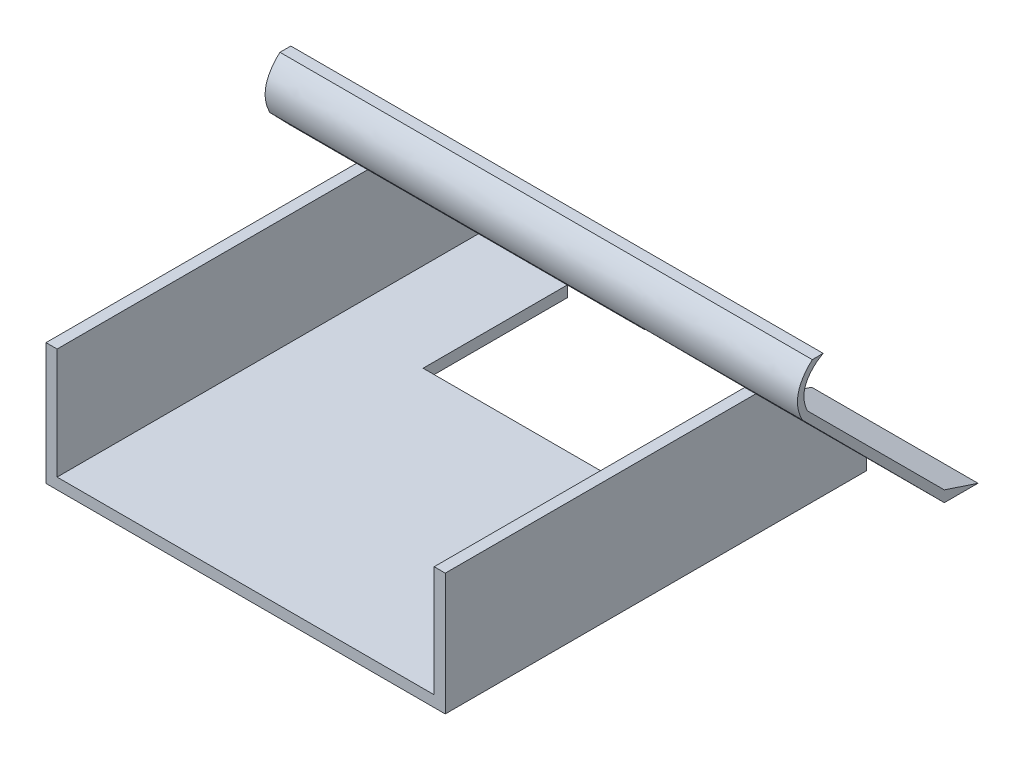
SolidWorks part; units mm, degrees
ref_plane "Front Plane" through (0, 0, 0) normal (0, 0, 1) x (1, 0, 0)
ref_plane "Top Plane" through (0, 0, 0) normal (0, 1, 0) x (1, 0, 0)
ref_plane "Right Plane" through (0, 0, 0) normal (1, 0, 0) x (0, 0, -1)
sketch "Sketch2" plane through (0, 0, 0) normal (0, 1, 0) x (1, 0, 0)
  line L1 (-90, 95) -> (90, 95)
  line L2 (-90, 95) -> (-90, -95)
  line L3 (-90, -95) -> (90, -95)
  line L4 (90, 95) -> (90, -95)
  line L5 (-90, 95) -> (90, -95) construction
  line L6 (-90, -95) -> (90, 95) construction
  point P0 (0, 0)
  dimension "D1" = 180
  dimension "D2" = 190
extrude "Boss-Extrude3" add sketch "Sketch2" along normal blind 5
sketch "Sketch4" plane through (0, 5, 0) normal (0, 1, 0) x (1, 0, 0)
  line L0 (-90, -95) -> (90, -95) construction
  line L3 (-90, 95) -> (-85, 95)
  line L4 (-90, 95) -> (-90, -95)
  line L5 (-90, -95) -> (-85, -95)
  line L6 (-85, 95) -> (-85, -95)
  line L8 (90, 95) -> (85, 95)
  line L9 (90, 95) -> (90, -95)
  line L10 (90, -95) -> (85, -95)
  line L11 (85, 95) -> (85, -95)
  dimension "D1" = 5
  dimension "D2" = 5
extrude "Boss-Extrude4" add sketch "Sketch4" along normal blind 50
sketch "Sketch5" plane through (-90, 0, 0) normal (-1, 0, 0) x (0, 0, 1)
  line L0 (-95, 5) -> (-45, 55)
  line L1 (-95, 55) -> (95, 55) construction
  line L2 (-45, 55) -> (-95, 55)
  line L3 (-95, 55) -> (-95, 5)
extrude "Cut-Extrude1" cut sketch "Sketch5" against normal blind 213
sketch "Sketch6" plane through (-90, 0, 0) normal (-1, 0, 0) x (0, 0, 1)
  line L0 (-45, 55) -> (-100, 0)
  line L1 (99, 0) -> (-99, 0) construction
  line L2 (-100, 0) -> (-115.1796, 0)
  line L3 (-115.1796, 0) -> (-100, 5)
  line L4 (-100, 5) -> (-38.2898, 66.7102)
  line L5 (-38.2898, 66.7102) -> (-35.9329, 64.3534)
  line L6 (-35.9329, 64.3534) -> (-45, 55)
extrude "Boss-Extrude8" add sketch "Sketch6" against normal blind 45 and the other way blind 30 separate body
sketch "Sketch7" plane through (0, 0, -95) normal (0, 0, -1) x (-1, 0, 0)
  line L0 (-85, 5) -> (85, 5) construction
  line L1 (-45, 5) -> (45, 5)
  line L2 (-45, 5) -> (-45, 0)
  line L3 (-45, 0) -> (45, 0)
  line L4 (45, 5) -> (45, 0)
  line L5 (99, 0) -> (-99, 0) construction
  line L6 (45, 5) -> (45, 0) construction
  line L9 (-90, 5) -> (-90, 0)
  line L10 (-90, 0) -> (-45, 0)
  dimension "D1" = 90
sketch "Sketch8" plane through (0, 5, 0) normal (0, 1, 0) x (1, 0, 0)
  line L0 (45, 95) -> (-45, 95) construction
  line L1 (-45, 95) -> (45, 95)
  line L2 (-45, 95) -> (-45, 30)
  line L3 (-45, 30) -> (45, 30)
  line L4 (45, 95) -> (45, 30)
  dimension "D1" = 65
  dimension "D2" = 90
extrude "Cut-Extrude2" cut sketch "Sketch8" against normal blind 213
sketch "Sketch9" plane through (-45, 0, 0) normal (1, 0, 0) x (0, 0, -1)
  line L0 (38.2898, 66.7102) -> (45, 60)
  line L1 (38.2898, 66.7102) -> (100, 5) construction
  line L2 (45, 60) -> (40, 60)
  line L3 (100, 0) -> (45, 55) construction
  line L4 (40, 60) -> (35.9329, 64.3534)
  line L5 (35.9329, 64.3534) -> (38.2898, 66.7102)
  line L6 (99, 0) -> (-99, 0) construction
  dimension "D1" = 60
extrude "Boss-Extrude9" add sketch "Sketch9" along normal blind 90
sketch "Sketch10" plane through (45, 0, 0) normal (1, 0, 0) x (0, 0, -1)
  line L0 (38.2898, 66.7102) -> (100, 5)
  line L1 (100, 5) -> (115.1796, 0)
  line L2 (115.1796, 0) -> (100, 0)
  line L3 (99, 0) -> (-99, 0) construction
  line L4 (100, 0) -> (35.9329, 64.3534)
  line L5 (35.9329, 64.3534) -> (38.2898, 66.7102)
extrude "Boss-Extrude10" add sketch "Sketch10" along normal blind 75
sketch "Sketch11" plane through (-120, 0, 0) normal (-1, 0, 0) x (0, 0, 1)
  line L0 (-40.4708, 85.6245) -> (-45.3688, 85.6245)
  line L1 (-45.3688, 85.6245) -> (-42.582, 83.8511)
  line L8 (-45, 55) -> (-35.9329, 64.3534)
  line L9 (-35.9329, 64.3534) -> (-38.2898, 66.7102)
  line L10 (-38.2898, 66.7102) -> (-100, 5)
  line L11 (-100, 5) -> (-115.1796, 0)
  line L12 (-115.1796, 0) -> (-100, 0)
  line L13 (-100, 0) -> (-45, 55)
  line L15 (-35.9329, 64.3534) -> (-38.2898, 66.7102)
  spline S0 degree 2 poles (-35.9329, 64.3534) (-29.9996, 76.0268) (-40.4708, 85.6245) knots 0 0 0 1 1 1
  spline S1 degree 2 poles (-38.2898, 66.7102) (-33.6123, 76.5047) (-42.582, 83.8511) knots 0 0 0 1 1 1
  dimension "D1" = 0
extrude "Boss-Extrude11" add sketch "Sketch11" against normal blind 240
